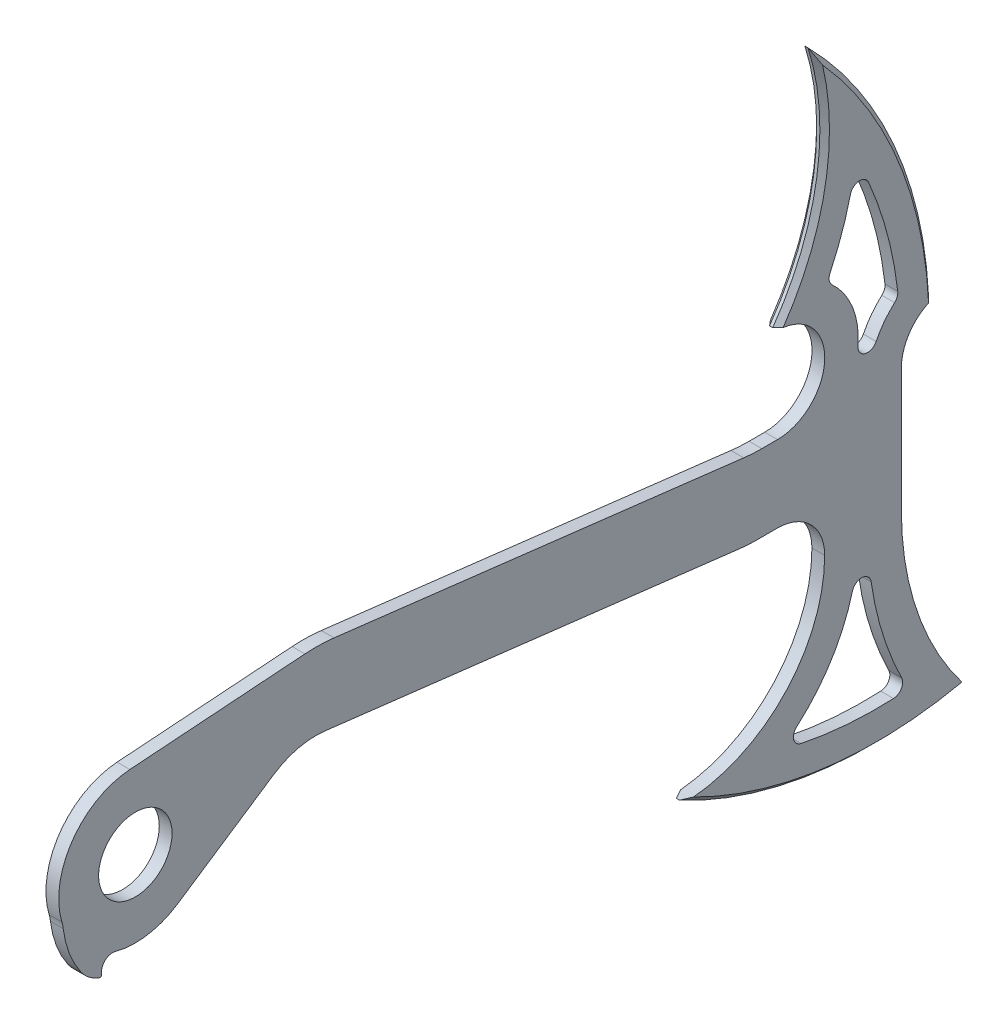
SolidWorks part; units mm, degrees
material "Plain Carbon Steel"
ref_plane "Front Plane" through (0, 0, 0) normal (0, 0, 1) x (1, 0, 0)
ref_plane "Top Plane" through (0, 0, 0) normal (0, 1, 0) x (1, 0, 0)
ref_plane "Right Plane" through (0, 0, 0) normal (1, 0, 0) x (0, 0, -1)
sketch "Sketch1" plane through (0, 0, 0) normal (1, 0, 0) x (0, 0, -1)
  line L0 (609.6, -38.1) -> (188.6392, 12.1626)
  line L1 (65.9911, 38.1) -> (762, 38.1)
  line L2 (65.9911, 38.1) -> (65.9911, -38.1)
  line L3 (65.9911, -38.1) -> (762, -38.1)
  line L4 (762, 38.1) -> (762, -38.1)
  line L5 (-5.4573, 76.0043) -> (168.6905, 88.5087)
  line L6 (42.2336, -63.4252) -> (137.3715, -0.0748)
  line L7 (197.6733, 87.8252) -> (614.133, 38.1)
  line L8 (614.133, 38.1) -> (605.0989, -37.5626) construction
  circle A0 centre (0, 0) radius 36.5125
  circle A1 centre (0, 0) radius 76.2
  circle A2 centre (179.6051, -63.5) radius 76.2
  circle A3 centre (179.6051, -63.5) radius 152.4
  dimension "D1" = 762
  dimension "D2" = 152.4
  dimension "D3" = 73.025
  dimension "D5" = 152.4
  dimension "D6" = 76.2
  dimension "D4" = 76.2
  dimension "D7" = 609.6
extrude "Boss-Extrude1" add sketch "Sketch1" along normal blind 12.7 contours A3 L2 A1 A0 | L2 A3 A1 | A1 L6 L3 | L0 A3 L1 A1 L3 L6 A2 | A1 A3 L2 | A3 L5 A1 L1 | L1 A3 | A3 L1 L7 | L8 L1 A3 L0 | L1 L8 L0 L3 L4
sketch "Sketch2" plane through (12.7, 0, 0) normal (1, 0, 0) x (0, 0, -1)
  line L5 (762, -38.1) -> (711.2, -38.1)
  line L10 (762, 38.1) -> (762, -38.1) construction
  arc A0 (762, -38.1) -> (838.2, -241.3) centre (1071.0333, -38.1) ccw
  arc A1 (711.2, -38.1) -> (558.8, -215.9) centre (508.9072, -18.9204) cw
  arc A2 (558.8, -215.9) -> (838.2, -241.3) centre (714.8418, -48.8404) ccw
  dimension "D10" = 228.6
  dimension "D8" = 203.2
  dimension "D5" = 203.2
  dimension "D6" = 177.8
  dimension "D7" = 50.8
  dimension "D9" = 152.4
  dimension "D11" = 76.2
extrude "Boss-Extrude2" add sketch "Sketch2" against normal blind 12.7
fillet "Fillet2" radius 50.8 1 edges at (6.35, -38.1, -711.2)
sketch "Sketch5" plane through (12.7, 0, 0) normal (1, 0, 0) x (0, 0, -1)
  line L0 (714.1404, -88.9) -> (746.9068, -88.9)
  line L10 (644.2904, -88.9) -> (746.9068, -88.9) construction
  arc A14 (742.95, -38.1) -> (809.2833, -235.9019) centre (1071.0333, -38.1) ccw
  arc A15 (597.7653, -222.6342) -> (809.2833, -235.9019) centre (714.8418, -48.8404) ccw
  arc A16 (597.7653, -222.6342) -> (706.3411, -120.974) centre (508.9072, -18.9204) ccw
  arc A17 (706.3411, -120.974) -> (644.2904, -19.05) centre (644.2904, -88.9) ccw
  arc A18 (746.9068, -88.9) -> (809.2833, -235.9019) centre (1071.0333, -38.1) ccw
  arc A19 (597.7653, -222.6342) -> (809.2833, -235.9019) centre (714.8418, -48.8404) ccw
  arc A20 (597.7653, -222.6342) -> (706.3411, -120.974) centre (508.9072, -18.9204) ccw
  arc A21 (706.3411, -120.974) -> (714.1404, -88.9) centre (644.2904, -88.9) ccw
  dimension "D1" = 19.05
extrude "Cut-Extrude3" cut sketch "Sketch5" against normal through all contours A21 A20 A19 A18 L0
sketch "Sketch6" plane through (12.7, 0, 0) normal (1, 0, 0) x (0, 0, -1)
  line L0 (714.1404, -88.9) -> (746.9068, -88.9) construction
  line L1 (730.5236, -88.9) -> (714.1404, -88.9)
  line L2 (730.5236, -88.9) -> (746.9068, -88.9)
  line L3 (714.1404, -88.9) -> (746.9068, -88.9) construction
  arc A1 (597.7653, -222.6342) -> (809.2833, -235.9019) centre (714.8418, -48.8404) ccw construction
  arc A2 (706.3411, -120.974) -> (714.1404, -88.9) centre (644.2904, -88.9) ccw construction
  arc A3 (701.7233, -257.9793) -> (809.2833, -235.9019) centre (714.8418, -48.8404) ccw
  arc A4 (597.7653, -222.6342) -> (701.7233, -257.9793) centre (714.8418, -48.8404) ccw
  arc A5 (722.332, -88.9) -> (647.3881, -247.2369) centre (480.1965, -71.1973) cw
  arc A7 (730.5236, -88.9) -> (701.7233, -257.9793) centre (309.0609, -104.1024) cw
  arc A9 (738.7152, -88.9) -> (756.9751, -254.1109) centre (8411.2548, 675.4907) ccw
  arc A10 (647.3881, -247.2369) -> (630.9607, -261.4948) centre (480.1965, -71.1973) cw
  arc A13 (558.8, -215.9) -> (838.2, -241.3) centre (714.8418, -48.8404) ccw construction
  arc A14 (701.7233, -257.9793) -> (693.9587, -276.4845) centre (309.0609, -104.1024) cw
  arc A15 (756.9751, -254.1109) -> (759.2555, -273.0844) centre (-6897.3047, -1183.7125) cw
  arc A16 (715.9989, -88.437) -> (643.0152, -242.6326) centre (480.1965, -71.1973) cw
  arc A17 (643.0152, -242.6326) -> (627.0174, -256.5176) centre (480.1965, -71.1973) cw
  arc A18 (724.1777, -89.1289) -> (695.8111, -255.6624) centre (309.0609, -104.1024) cw
  arc A19 (695.8111, -255.6624) -> (688.1634, -273.889) centre (309.0609, -104.1024) cw
  arc A20 (732.3965, -89.5295) -> (750.6714, -254.8765) centre (8411.2548, 675.4907) ccw
  arc A21 (750.6714, -254.8765) -> (752.95, -273.8343) centre (-6897.3047, -1183.7125) cw
  arc A22 (728.6651, -89.363) -> (651.761, -251.8413) centre (480.1965, -71.1973) cw
  arc A23 (651.761, -251.8413) -> (634.9039, -266.4721) centre (480.1965, -71.1973) cw
  arc A24 (736.8695, -88.6711) -> (707.6356, -260.2962) centre (309.0609, -104.1024) cw
  arc A25 (707.6356, -260.2962) -> (699.754, -279.08) centre (309.0609, -104.1024) cw
  arc A26 (745.0339, -88.2705) -> (763.2787, -253.3453) centre (8411.2548, 675.4907) ccw
  arc A27 (763.2787, -253.3453) -> (765.5611, -272.3344) centre (-6897.3047, -1183.7125) cw
  point P0 (701.7233, -257.9793)
  point P9 (647.3881, -247.2369)
  point P10 (756.9751, -254.1109)
  point P11 (730.5236, -88.9)
  point P18 (738.7152, -88.9)
  point P20 (749.3331, -188.8664)
  point P21 (721.941, -190.079)
  point P22 (695.2221, -183.9226)
  point P23 (722.332, -88.9)
  dimension "D1" = 6.35
  dimension "D2" = 6.35
extrude "Boss-Extrude3" add sketch "Sketch6" against normal up to surface (12.7 mm away) up to face at (0, 0, -36.5125)
sketch "Sketch9" plane through (12.7, 0, 0) normal (1, 0, 0) x (0, 0, -1)
  line L0 (714.1404, -88.9) -> (715.9646, -88.9) construction
  line L1 (745.0966, -88.9) -> (746.9068, -88.9) construction
  line L2 (714.1404, -88.9) -> (715.9646, -88.9)
  line L3 (745.0966, -88.9) -> (746.9068, -88.9)
  line L10 (168.6905, 88.5087) -> (-5.4573, 76.0043)
  line L11 (42.2336, -63.4252) -> (137.3715, -0.0748)
  line L12 (188.6392, 12.1626) -> (609.6, -38.1)
  line L13 (609.6, -38.1) -> (644.2904, -38.1)
  line L14 (762, -38.1) -> (762, 38.1)
  line L18 (762, 38.1) -> (614.133, 38.1)
  line L19 (614.133, 38.1) -> (197.6733, 87.8252)
  line L20 (168.6905, 88.5087) -> (-5.4573, 76.0043)
  line L21 (42.2336, -63.4252) -> (137.3715, -0.0748)
  line L22 (188.6392, 12.1626) -> (609.6, -38.1)
  line L23 (609.6, -38.1) -> (644.2904, -38.1)
  line L24 (762, -38.1) -> (762, 38.1)
  line L28 (762, 38.1) -> (614.133, 38.1)
  line L29 (614.133, 38.1) -> (197.6733, 87.8252)
  circle A0 centre (701.8763, -138.4929) radius 4.7625
  circle A1 centre (719.7422, -147.8567) radius 2.3812
  circle A2 centre (736.6639, -153.685) radius 2.3812
  circle A3 centre (755.6256, -144.4218) radius 4.7625
  arc A4 (597.7653, -222.6342) -> (706.3411, -120.974) centre (508.9072, -18.9204) ccw construction
  arc A5 (640.6741, -244.826) -> (715.9646, -88.9) centre (480.1965, -71.1973) ccw construction
  arc A6 (654.2542, -249.4403) -> (724.0537, -122.1907) centre (480.1965, -71.1973) ccw construction
  arc A7 (695.1024, -257.4586) -> (724.0537, -122.1907) centre (309.0609, -104.1024) ccw construction
  arc A8 (708.4153, -258.2918) -> (736.426, -128.9495) centre (309.0609, -104.1024) ccw construction
  arc A9 (736.426, -128.9495) -> (750.6714, -254.8765) centre (8411.2548, 675.4907) ccw construction
  arc A10 (745.0966, -88.9) -> (763.2044, -252.7331) centre (8411.2548, 675.4907) ccw construction
  arc A13 (597.7653, -222.6342) -> (706.3411, -120.974) centre (508.9072, -18.9204) ccw
  arc A14 (706.3411, -120.974) -> (714.1404, -88.9) centre (644.2904, -88.9) ccw
  arc A15 (640.6741, -244.826) -> (715.9646, -88.9) centre (480.1965, -71.1973) ccw
  arc A16 (654.2542, -249.4403) -> (724.0537, -122.1907) centre (480.1965, -71.1973) ccw
  arc A17 (695.1024, -257.4586) -> (724.0537, -122.1907) centre (309.0609, -104.1024) ccw
  arc A18 (708.4153, -258.2918) -> (736.426, -128.9495) centre (309.0609, -104.1024) ccw
  arc A19 (736.426, -128.9495) -> (750.6714, -254.8765) centre (8411.2548, 675.4907) ccw
  arc A20 (746.9068, -88.9) -> (809.2833, -235.9019) centre (1071.0333, -38.1) ccw
  arc A21 (-5.4573, 76.0043) -> (42.2336, -63.4252) centre (0, 0) ccw
  arc A23 (188.6392, 12.1626) -> (137.3715, -0.0748) centre (179.6051, -63.5) ccw
  arc A24 (689.4182, -112.2265) -> (644.2904, -38.1) centre (644.2904, -88.9) ccw
  arc A25 (558.8, -215.9) -> (689.4182, -112.2265) centre (508.9072, -18.9204) ccw
  arc A26 (558.8, -215.9) -> (838.2, -241.3) centre (714.8418, -48.8404) ccw
  arc A27 (762, -38.1) -> (838.2, -241.3) centre (1071.0333, -38.1) ccw
  arc A29 (197.6733, 87.8252) -> (168.6905, 88.5087) centre (179.6051, -63.5) ccw
  arc A30 (-5.4573, 76.0043) -> (42.2336, -63.4252) centre (0, 0) ccw
  arc A32 (188.6392, 12.1626) -> (137.3715, -0.0748) centre (179.6051, -63.5) ccw
  arc A33 (689.4182, -112.2265) -> (644.2904, -38.1) centre (644.2904, -88.9) ccw
  arc A34 (558.8, -215.9) -> (689.4182, -112.2265) centre (508.9072, -18.9204) ccw
  arc A35 (558.8, -215.9) -> (838.2, -241.3) centre (714.8418, -48.8404) ccw
  arc A36 (762, -38.1) -> (838.2, -241.3) centre (1071.0333, -38.1) ccw
  arc A38 (197.6733, 87.8252) -> (168.6905, 88.5087) centre (179.6051, -63.5) ccw
  arc A39 (745.0966, -88.9) -> (763.2044, -252.7331) centre (8411.2548, 675.4907) ccw
  dimension "D1" = 9.525
  dimension "D3" = 4.7625
  dimension "D2" = 0
extrude "Boss-Extrude4" add sketch "Sketch9" against normal up to surface (12.7 mm away)
fillet "Fillet3" radius 152.4 2 edges at (6.35, -38.1, -609.6) (6.35, 38.1, -614.133)
sketch "Sketch12" plane through (12.7, 0, 0) normal (1, 0, 0) x (0, 0, -1)
  line L0 (0, 0) -> (-25.4743, -95.0712) construction
  line L1 (0, 0) -> (0, -76.2) construction
  line L2 (-33.332, -81.4613) -> (-22.5981, -84.3374) construction
  line L3 (0, 0) -> (-47.625, -82.4889) construction
  arc A0 (-25.4743, -95.0712) -> (-19.722, -73.6035) centre (-22.5981, -84.3374) cw
  arc A1 (-5.4573, 76.0043) -> (42.2336, -63.4252) centre (0, 0) ccw construction
  circle A2 centre (0, 0) radius 95.25
  arc A3 (-72.0991, -24.661) -> (-47.625, -82.4889) centre (29.1237, -15.9142) ccw
  arc A4 (-72.0991, -24.661) -> (-19.722, -73.6035) centre (0, 0) ccw
  dimension "D1" = 22.225
  dimension "D3" = 15
  dimension "D4" = 101.6
  dimension "D2" = 15
  dimension "D5" = 95.25
extrude "Boss-Extrude7" add sketch "Sketch12" against normal up to surface (12.7 mm away) contours A4 A3 A2 A0
fillet "Fillet7" radius 1.5875 1 edges at (6.35, -89.5694, 32.4019)
fillet "Fillet8" radius 38.1 2 edges at (6.35, -24.661, 72.0991) (6.35, -82.4889, 47.625)
sketch "Sketch15" plane through (12.7, 0, 0) normal (1, 0, 0) x (0, 0, -1)
  line L0 (762, 38.1) -> (762, -38.1) construction
  line L1 (623.1991, 38.1) -> (762, 38.1) construction
  line L3 (638.81, 38.1) -> (762, 38.1)
  line L4 (685.8, 85.09) -> (685.8, 38.1) construction
  circle A0 centre (0, 0) radius 762
  arc A1 (762, 38.1) -> (793.75, 82.55) centre (808.99, 38.1) cw
  arc A2 (673.9382, 355.6) -> (793.75, 82.55) centre (375.1694, 61.6918) cw
  circle A3 centre (638.81, 85.09) radius 46.99
  arc A4 (638.81, 132.08) -> (673.9382, 355.6) centre (431.7174, 279.1468) ccw
  point P5 (673.9382, 355.6)
  line M31 (762, 38.1) -> (623.1991, 38.1)
  dimension "D1" = 317.5
  dimension "D2" = 44.45
  dimension "D4" = 76.2
  dimension "D5" = 254
  dimension "D6" = 419.1
  dimension "D3" = 31.75
extrude "Boss-Extrude10" add sketch "Sketch15" against normal up to surface (12.7 mm away) contours A4 A3 L3 A0 | A2 A0 A1 M31 | L4 A3 M31
sketch "Sketch16" plane through (12.7, 0, 0) normal (1, 0, 0) x (0, 0, -1)
  line L2 (728.6625, 38.1) -> (728.6625, -38.1)
  line L3 (728.6625, 38.1) -> (728.6625, -38.1)
  arc A14 (718.8696, 78.5349) -> (736.9099, 73.5537) centre (728.3628, 77.7577) ccw
  arc A18 (638.81, 4.7625) -> (687.7733, 148.7697) centre (638.81, 85.09) ccw
  arc A19 (758.9319, 100.9227) -> (728.6625, 38.1) centre (808.99, 38.1) ccw
  arc A20 (758.9319, 100.9227) -> (716.555, 241.3264) centre (375.1694, 61.6918) ccw
  arc A21 (687.7733, 148.7697) -> (716.555, 241.3264) centre (431.7174, 279.1468) ccw
  arc A22 (638.81, 4.7625) -> (687.7733, 148.7697) centre (638.81, 85.09) ccw
  arc A23 (758.9319, 100.9227) -> (728.6625, 38.1) centre (808.99, 38.1) ccw
  arc A24 (758.9319, 100.9227) -> (716.555, 241.3264) centre (375.1694, 61.6918) ccw
  arc A25 (687.7733, 148.7697) -> (716.555, 241.3264) centre (431.7174, 279.1468) ccw
  dimension "D2" = 9.525
  dimension "D1" = 33.3375
extrude "Cut-Extrude4" cut sketch "Sketch16" against normal through all contours A25 A22 A14 A23 A24
chamfer "Chamfer3" distance 4.7625 angle 45 6 edges at (0, 230.0907, -758.9488) (0, 239.7125, -682.6375) (12.7, 239.7125, -682.6375) (12.7, 230.0907, -758.9488) (12.7, -276.5016, -694.1453) (0, -276.5016, -694.1453)
sketch "Sketch17" plane through (12.7, 0, 0) normal (1, 0, 0) x (0, 0, -1)
  line L0 (644.2904, -38.1) -> (762, -38.1)
  line L1 (762, -38.1) -> (838.2, -241.3)
  line L5 (558.8, -215.9) -> (644.2904, -38.1)
  arc A0 (558.8, -215.9) -> (838.2, -241.3) centre (714.8418, -48.8404) ccw
extrude "Cut-Extrude5" cut sketch "Sketch17" against normal through all
sketch "Sketch20" plane through (12.7, 0, 0) normal (1, 0, 0) x (0, 0, -1)
  line L0 (762, -38.1) -> (762, -85.09)
  line L1 (618.6661, -38.1) -> (762, -38.1) construction
  line L2 (685.7167, 82.293) -> (685.7167, -85.09) construction
  line L3 (685.7167, -85.09) -> (762, -85.09) construction
  line L5 (638.7267, -38.1) -> (762, -38.1)
  circle A0 centre (638.7267, -85.09) radius 46.99
  arc A1 (638.81, 38.1) -> (644.394, 131.747) centre (638.81, 85.09) ccw construction
  arc A2 (762, -85.09) -> (825.5, -266.7) centre (1053.4523, -85.09) ccw
  arc A3 (825.5, -266.7) -> (546.0167, -228.6) centre (737.2408, 130.0005) cw
  arc A4 (546.0167, -228.6) -> (685.7167, -85.09) centre (542.1547, -85.09) ccw
  line M1 (618.6661, -38.1) -> (762, -38.1)
  dimension "D1" = 63.5
  dimension "D2" = 139.7
  dimension "D3" = 406.4
  dimension "D4" = 228.6
  dimension "D5" = 190.5
extrude "Boss-Extrude12" add sketch "Sketch20" against normal up to surface (12.7 mm away) contours A4 A3 A2 L0 A0 M1 up to face at (0, 38.0919, -65.9984)
sketch "Sketch21" plane through (12.7, 0, 0) normal (1, 0, 0) x (0, 0, -1)
  line L14 (618.6661, -4.7625) -> (638.7267, -4.7625)
  line L15 (728.6625, -85.09) -> (728.6625, 38.1)
  line L16 (638.81, 4.7625) -> (623.1991, 4.7625)
  line L17 (601.1785, 6.0725) -> (193.7209, 54.7228)
  line L18 (171.078, 55.2568) -> (-3.0698, 42.7524)
  line L19 (23.7564, -35.6767) -> (118.8943, 27.6738)
  line L20 (192.5916, 45.265) -> (604.5503, -3.9228)
  line L21 (618.6661, -4.7625) -> (638.7267, -4.7625)
  line L22 (728.6625, -85.09) -> (728.6625, 38.1)
  line L23 (638.81, 4.7625) -> (623.1991, 4.7625)
  line L24 (601.1785, 6.0725) -> (193.7209, 54.7228)
  line L25 (171.078, 55.2568) -> (-3.0698, 42.7524)
  line L26 (23.7564, -35.6767) -> (118.8943, 27.6738)
  line L27 (192.5916, 45.265) -> (604.5503, -3.9228)
  arc A20 (713.2788, -129.9226) -> (731.9223, -130.9904) centre (722.4929, -132.3365) cw
  arc A21 (718.8696, 78.5349) -> (736.9099, 73.5537) centre (728.3628, 77.7577) ccw construction
  arc A40 (719.0542, -85.09) -> (638.7267, -4.7625) centre (638.7267, -85.09) ccw
  arc A41 (642.4409, -230.8161) -> (719.0542, -85.09) centre (542.1547, -85.09) ccw
  arc A42 (642.4409, -230.8161) -> (768.9225, -241.7143) centre (737.2408, 130.0005) ccw
  arc A43 (728.6625, -85.09) -> (768.9225, -241.7143) centre (1053.4523, -85.09) ccw
  arc A44 (754.5171, 97.1357) -> (728.6625, 38.1) centre (808.99, 38.1) ccw
  arc A45 (754.5171, 97.1357) -> (718.9354, 225.9658) centre (375.1694, 61.6918) ccw
  arc A46 (691.5443, 145.6837) -> (718.9354, 225.9658) centre (431.7174, 279.1468) ccw
  arc A47 (638.81, 4.7625) -> (691.5443, 145.6837) centre (638.81, 85.09) ccw
  arc A48 (601.1785, 6.0725) -> (623.1991, 4.7625) centre (623.1991, 190.5) ccw
  arc A49 (193.7209, 54.7228) -> (171.078, 55.2568) centre (179.6051, -63.5) ccw
  arc A50 (-3.0698, 42.7524) -> (-41.0971, -12.1746) centre (0, 0) ccw
  arc A51 (-38.658, -24.0018) -> (-41.0971, -12.1746) centre (-109.5923, -32.4656) ccw
  arc A52 (-38.658, -24.0018) -> (-34.1922, -41.4261) centre (29.1237, -15.9142) ccw
  arc A53 (-11.0936, -41.402) -> (-34.1922, -41.4261) centre (-22.5981, -84.3374) ccw
  arc A54 (-11.0936, -41.402) -> (23.7564, -35.6767) centre (0, 0) ccw
  arc A55 (192.5916, 45.265) -> (118.8943, 27.6738) centre (179.6051, -63.5) ccw
  arc A56 (604.5503, -3.9228) -> (618.6661, -4.7625) centre (618.6661, 114.3) ccw
  arc A57 (719.0542, -85.09) -> (638.7267, -4.7625) centre (638.7267, -85.09) ccw
  arc A58 (642.4409, -230.8161) -> (719.0542, -85.09) centre (542.1547, -85.09) ccw
  arc A59 (642.4409, -230.8161) -> (768.9225, -241.7143) centre (737.2408, 130.0005) ccw
  arc A60 (728.6625, -85.09) -> (768.9225, -241.7143) centre (1053.4523, -85.09) ccw
  arc A61 (754.5171, 97.1357) -> (728.6625, 38.1) centre (808.99, 38.1) ccw
  arc A62 (754.5171, 97.1357) -> (718.9354, 225.9658) centre (375.1694, 61.6918) ccw
  arc A63 (691.5443, 145.6837) -> (718.9354, 225.9658) centre (431.7174, 279.1468) ccw
  arc A64 (638.81, 4.7625) -> (691.5443, 145.6837) centre (638.81, 85.09) ccw
  arc A65 (601.1785, 6.0725) -> (623.1991, 4.7625) centre (623.1991, 190.5) ccw
  arc A66 (193.7209, 54.7228) -> (171.078, 55.2568) centre (179.6051, -63.5) ccw
  arc A67 (-3.0698, 42.7524) -> (-41.0971, -12.1746) centre (0, 0) ccw
  arc A68 (-38.658, -24.0018) -> (-41.0971, -12.1746) centre (-109.5923, -32.4656) ccw
  arc A69 (-38.658, -24.0018) -> (-34.1922, -41.4261) centre (29.1237, -15.9142) ccw
  arc A70 (-11.0936, -41.402) -> (-34.1922, -41.4261) centre (-22.5981, -84.3374) ccw
  arc A71 (-11.0936, -41.402) -> (23.7564, -35.6767) centre (0, 0) ccw
  arc A72 (192.5916, 45.265) -> (118.8943, 27.6738) centre (179.6051, -63.5) ccw
  arc A73 (604.5503, -3.9228) -> (618.6661, -4.7625) centre (618.6661, 114.3) ccw
  dimension "D1" = 33.3375
extrude "Cut-Extrude7" cut sketch "Sketch21" against normal through all contours A60 A20 A58 A59
fillet "Fillet9" radius 9.525 5 edges at (6.35, 241.3264, -716.555) (6.35, 100.9227, -758.9319) (6.35, 148.7697, -687.7733) (6.35, -241.7143, -768.9225) (6.35, -230.8161, -642.4409)
chamfer "Chamfer5" distance 4.7625 angle 45 2 edges at (0, -272.6751, -682.3468) (12.7, -272.6751, -682.3468)
